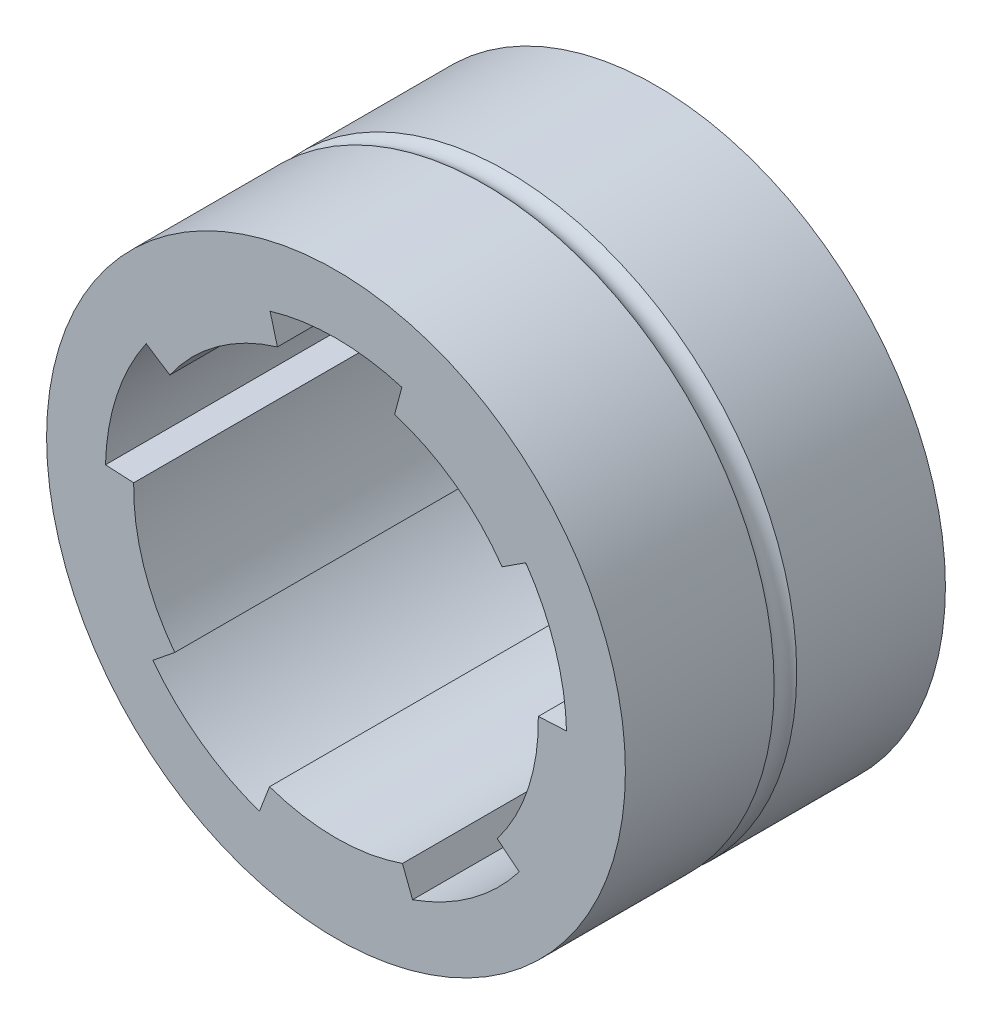
SolidWorks part; units mm, degrees
ref_plane "Front Plane" through (0, 0, 0) normal (0, 0, 1) x (1, 0, 0)
ref_plane "Top Plane" through (0, 0, 0) normal (0, 1, 0) x (1, 0, 0)
ref_plane "Right Plane" through (0, 0, 0) normal (1, 0, 0) x (0, 0, -1)
sketch "Sketch1" plane through (0, 0, 0) normal (0, 0, 1) x (1, 0, 0)
  line L10 (-17.6491, 12.2784) -> (-20.1651, 13.9123)
  line L11 (-24.4914, 0.5975) -> (-21.4955, 0.4405)
  line L12 (-17.1313, -12.9911) -> (-19.4627, -14.8791)
  line L13 (-8.1365, -23.108) -> (-7.0614, -20.3073)
  line L14 (7.0614, -20.3073) -> (8.1365, -23.108)
  line L15 (19.4627, -14.8791) -> (17.1313, -12.9911)
  line L16 (21.4955, 0.4405) -> (24.4914, 0.5975)
  line L17 (20.1651, 13.9123) -> (17.6491, 12.2784)
  line L18 (6.2235, 20.5795) -> (7, 23.4773)
  line L19 (-7, 23.4773) -> (-6.2235, 20.5795)
  line L20 (-17.6491, 12.2784) -> (-20.1651, 13.9123)
  line L21 (-24.4914, 0.5975) -> (-21.4955, 0.4405)
  line L22 (-17.1313, -12.9911) -> (-19.4627, -14.8791)
  line L23 (-8.1365, -23.108) -> (-7.0614, -20.3073)
  line L24 (7.0614, -20.3073) -> (8.1365, -23.108)
  line L25 (19.4627, -14.8791) -> (17.1313, -12.9911)
  line L26 (21.4955, 0.4405) -> (24.4914, 0.5975)
  line L27 (20.1651, 13.9123) -> (17.6491, 12.2784)
  line L28 (6.2235, 20.5795) -> (7, 23.4773)
  line L29 (-7, 23.4773) -> (-6.2235, 20.5795)
  circle A0 centre (0, 0) radius 30.75
  arc A10 (-6.2235, 20.5795) -> (-17.6491, 12.2784) centre (0, 0) ccw
  arc A11 (-20.1651, 13.9123) -> (-24.4914, 0.5975) centre (0, 0) ccw
  arc A12 (-21.4955, 0.4405) -> (-17.1313, -12.9911) centre (0, 0) ccw
  arc A13 (-19.4627, -14.8791) -> (-8.1365, -23.108) centre (0, 0) ccw
  arc A14 (-7.0614, -20.3073) -> (7.0614, -20.3073) centre (0, 0) ccw
  arc A15 (8.1365, -23.108) -> (19.4627, -14.8791) centre (0, 0) ccw
  arc A16 (17.1313, -12.9911) -> (21.4955, 0.4405) centre (0, 0) ccw
  arc A17 (24.4914, 0.5975) -> (20.1651, 13.9123) centre (0, 0) ccw
  arc A18 (17.6491, 12.2784) -> (6.2235, 20.5795) centre (0, 0) ccw
  arc A19 (7, 23.4773) -> (-7, 23.4773) centre (0, 0) ccw
  arc A20 (-6.2235, 20.5795) -> (-17.6491, 12.2784) centre (0, 0) ccw
  arc A21 (-20.1651, 13.9123) -> (-24.4914, 0.5975) centre (0, 0) ccw
  arc A22 (-21.4955, 0.4405) -> (-17.1313, -12.9911) centre (0, 0) ccw
  arc A23 (-19.4627, -14.8791) -> (-8.1365, -23.108) centre (0, 0) ccw
  arc A24 (-7.0614, -20.3073) -> (7.0614, -20.3073) centre (0, 0) ccw
  arc A25 (8.1365, -23.108) -> (19.4627, -14.8791) centre (0, 0) ccw
  arc A26 (17.1313, -12.9911) -> (21.4955, 0.4405) centre (0, 0) ccw
  arc A27 (24.4914, 0.5975) -> (20.1651, 13.9123) centre (0, 0) ccw
  arc A28 (17.6491, 12.2784) -> (6.2235, 20.5795) centre (0, 0) ccw
  arc A29 (7, 23.4773) -> (-7, 23.4773) centre (0, 0) ccw
  dimension "D2" = 61.5
  dimension "D1" = 0
extrude "Boss-Extrude1" add sketch "Sketch1" against normal up to surface (34 mm away)
sketch "Sketch2" plane through (0, 0, 0) normal (-1, 0, 0) x (0, 0, 1)
  line L0 (-34, 30.75) -> (0, 30.75) construction
  line L1 (-18.2, 30.75) -> (-15.8, 30.75)
  line L2 (-17, 30.75) -> (-17, 43.7176) construction
  line L3 (0, 30.75) -> (-34, 30.75) construction
  line L4 (27.9535, 0) -> (-58.0827, 0) construction
  arc A1 (-18.2, 30.75) -> (-15.8, 30.75) centre (-17, 31.94) ccw
  dimension "D2" = 2.4
  dimension "D1" = 0.5
revolve "Cut-Revolve1" cut sketch "Sketch2" angle 360 about L4
sketch "Sketch3" [suppressed] plane through (0, 0, 0) normal (0, 0, 1) x (1, 0, 0)
  line L10 (-7, 26.0768) -> (-5.7059, 21.2472) construction
  line L11 (-18.444, 11.9924) -> (-22.6374, 14.7156) construction
  line L12 (-26.9636, 1.4008) -> (-21.9705, 1.1391) construction
  line L13 (-17.105, -13.8355) -> (-20.9907, -16.9821) construction
  line L14 (-9.6644, -25.2111) -> (-7.8726, -20.5432) construction
  line L15 (7.8726, -20.5432) -> (9.6644, -25.2111) construction
  line L16 (20.9907, -16.9821) -> (17.105, -13.8355) construction
  line L17 (21.9705, 1.1391) -> (26.9636, 1.4008) construction
  line L18 (22.6374, 14.7156) -> (18.444, 11.9924) construction
  line L19 (5.7059, 21.2472) -> (7, 26.0768) construction
  line L20 (6.3168, 21.5951) -> (7.6111, 26.4258)
  line L21 (22.7804, 15.4046) -> (18.5862, 12.6809)
  line L22 (22.4902, 0.6656) -> (27.4844, 0.9274)
  line L23 (21.6902, -16.9052) -> (17.8037, -13.7579)
  line L24 (7.5829, -21.1837) -> (9.3751, -25.8526)
  line L25 (-9.3751, -25.8526) -> (-7.5829, -21.1837)
  line L26 (-17.8037, -13.7579) -> (-21.6902, -16.9052)
  line L27 (-27.4844, 0.9274) -> (-22.4902, 0.6656)
  line L28 (-18.5862, 12.6809) -> (-22.7804, 15.4046)
  line L29 (-7.6111, 26.4258) -> (-6.3168, 21.5951)
  line L30 (6.3168, 21.5951) -> (7.6111, 26.4258)
  line L31 (22.7804, 15.4046) -> (18.5862, 12.6809)
  line L32 (22.4902, 0.6656) -> (27.4844, 0.9274)
  line L33 (21.6902, -16.9052) -> (17.8037, -13.7579)
  line L34 (7.5829, -21.1837) -> (9.3751, -25.8526)
  line L35 (-9.3751, -25.8526) -> (-7.5829, -21.1837)
  line L36 (-17.8037, -13.7579) -> (-21.6902, -16.9052)
  line L37 (-27.4844, 0.9274) -> (-22.4902, 0.6656)
  line L38 (-18.5862, 12.6809) -> (-22.7804, 15.4046)
  line L39 (-7.6111, 26.4258) -> (-6.3168, 21.5951)
  line L40 (-7, 26.0768) -> (-5.7059, 21.2472)
  line L41 (-18.444, 11.9924) -> (-22.6374, 14.7156)
  line L42 (-26.9636, 1.4008) -> (-21.9705, 1.1391)
  line L43 (-17.105, -13.8355) -> (-20.9907, -16.9821)
  line L44 (-9.6644, -25.2111) -> (-7.8726, -20.5432)
  line L45 (7.8726, -20.5432) -> (9.6644, -25.2111)
  line L46 (20.9907, -16.9821) -> (17.105, -13.8355)
  line L47 (21.9705, 1.1391) -> (26.9636, 1.4008)
  line L48 (22.6374, 14.7156) -> (18.444, 11.9924)
  line L49 (5.7059, 21.2472) -> (7, 26.0768)
  arc A10 (-5.7059, 21.2472) -> (-18.444, 11.9924) centre (0, 0) ccw construction
  arc A11 (-22.6374, 14.7156) -> (-26.9636, 1.4008) centre (0, 0) ccw construction
  arc A12 (-21.9705, 1.1391) -> (-17.105, -13.8355) centre (0, 0) ccw construction
  arc A13 (-20.9907, -16.9821) -> (-9.6644, -25.2111) centre (0, 0) ccw construction
  arc A14 (-7.8726, -20.5432) -> (7.8726, -20.5432) centre (0, 0) ccw construction
  arc A15 (9.6644, -25.2111) -> (20.9907, -16.9821) centre (0, 0) ccw construction
  arc A16 (17.105, -13.8355) -> (21.9705, 1.1391) centre (0, 0) ccw construction
  arc A17 (26.9636, 1.4008) -> (22.6374, 14.7156) centre (0, 0) ccw construction
  arc A18 (18.444, 11.9924) -> (5.7059, 21.2472) centre (0, 0) ccw construction
  arc A19 (7, 26.0768) -> (-7, 26.0768) centre (0, 0) ccw construction
  arc A20 (18.5862, 12.6809) -> (6.3168, 21.5951) centre (0, 0) ccw
  arc A21 (27.4844, 0.9274) -> (22.7804, 15.4046) centre (0, 0) ccw
  arc A22 (17.8037, -13.7579) -> (22.4902, 0.6656) centre (0, 0) ccw
  arc A23 (9.3751, -25.8526) -> (21.6902, -16.9052) centre (0, 0) ccw
  arc A24 (-7.5829, -21.1837) -> (7.5829, -21.1837) centre (0, 0) ccw
  arc A25 (-21.6902, -16.9052) -> (-9.3751, -25.8526) centre (0, 0) ccw
  arc A26 (-22.4902, 0.6656) -> (-17.8037, -13.7579) centre (0, 0) ccw
  arc A27 (-22.7804, 15.4046) -> (-27.4844, 0.9274) centre (0, 0) ccw
  arc A28 (-6.3168, 21.5951) -> (-18.5862, 12.6809) centre (0, 0) ccw
  arc A29 (7.6111, 26.4258) -> (-7.6111, 26.4258) centre (0, 0) ccw
  arc A30 (18.5862, 12.6809) -> (6.3168, 21.5951) centre (0, 0) ccw
  arc A31 (27.4844, 0.9274) -> (22.7804, 15.4046) centre (0, 0) ccw
  arc A32 (17.8037, -13.7579) -> (22.4902, 0.6656) centre (0, 0) ccw
  arc A33 (9.3751, -25.8526) -> (21.6902, -16.9052) centre (0, 0) ccw
  arc A34 (-7.5829, -21.1837) -> (7.5829, -21.1837) centre (0, 0) ccw
  arc A35 (-21.6902, -16.9052) -> (-9.3751, -25.8526) centre (0, 0) ccw
  arc A36 (-22.4902, 0.6656) -> (-17.8037, -13.7579) centre (0, 0) ccw
  arc A37 (-22.7804, 15.4046) -> (-27.4844, 0.9274) centre (0, 0) ccw
  arc A38 (-6.3168, 21.5951) -> (-18.5862, 12.6809) centre (0, 0) ccw
  arc A39 (7.6111, 26.4258) -> (-7.6111, 26.4258) centre (0, 0) ccw
  arc A40 (-5.7059, 21.2472) -> (-18.444, 11.9924) centre (0, 0) ccw
  arc A41 (-22.6374, 14.7156) -> (-26.9636, 1.4008) centre (0, 0) ccw
  arc A42 (-21.9705, 1.1391) -> (-17.105, -13.8355) centre (0, 0) ccw
  arc A43 (-20.9907, -16.9821) -> (-9.6644, -25.2111) centre (0, 0) ccw
  arc A44 (-7.8726, -20.5432) -> (7.8726, -20.5432) centre (0, 0) ccw
  arc A45 (9.6644, -25.2111) -> (20.9907, -16.9821) centre (0, 0) ccw
  arc A46 (17.105, -13.8355) -> (21.9705, 1.1391) centre (0, 0) ccw
  arc A47 (26.9636, 1.4008) -> (22.6374, 14.7156) centre (0, 0) ccw
  arc A48 (18.444, 11.9924) -> (5.7059, 21.2472) centre (0, 0) ccw
  arc A49 (7, 26.0768) -> (-7, 26.0768) centre (0, 0) ccw
  dimension "D1" = 0.5
extrude "Cut-Extrude1" [suppressed] cut sketch "Sketch3" against normal through all
